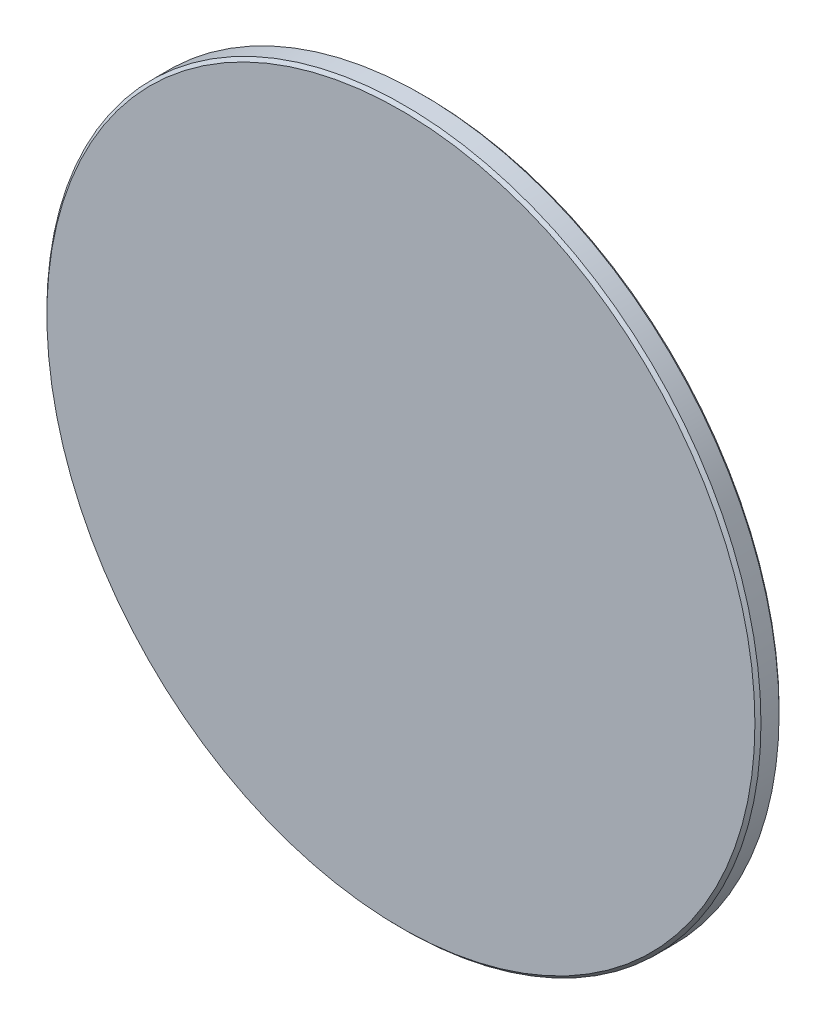
SolidWorks part; units mm, degrees
material "玻璃"
ref_plane "前视基准面" through (0, 0, 0) normal (0, 0, 1) x (1, 0, 0)
ref_plane "上视基准面" through (0, 0, 0) normal (0, 1, 0) x (1, 0, 0)
ref_plane "右视基准面" through (0, 0, 0) normal (1, 0, 0) x (0, 0, -1)
sketch "草图1" plane through (0, 0, 0) normal (0, 0, 1) x (1, 0, 0)
  circle A0 centre (0, 0) radius 59
extrude "凸台-拉伸1" add sketch "草图1" along normal blind 4 contours A0
chamfer "倒角1" distance 0.5 angle 45 2 edges at (59, 0, 0) (59, 0, 4)
